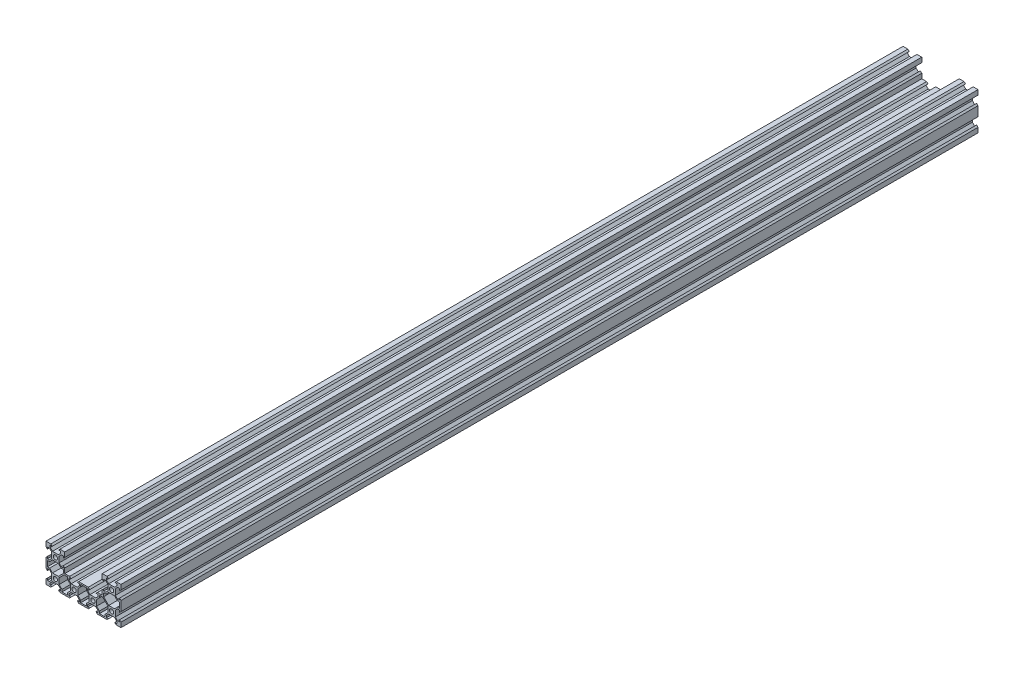
SolidWorks part; units mm, degrees
ref_plane "Front Plane" through (0, 0, 0) normal (0, 0, 1) x (1, 0, 0)
ref_plane "Top Plane" through (0, 0, 0) normal (0, 1, 0) x (1, 0, 0)
ref_plane "Right Plane" through (0, 0, 0) normal (1, 0, 0) x (0, 0, -1)
sketch "Sketch2" plane through (0, 0, 0) normal (0, 0, 1) x (1, 0, 0)
  line L0 (0, 10) -> (0, -10) construction
  line L1 (0, -10) -> (-40, -10)
  line L2 (-40, -10) -> (-40, 30)
  line L3 (-40, 30) -> (-20, 30)
  line L4 (-20, 30) -> (-20, 10)
  line L5 (-20, 10) -> (0, 10)
  line L6 (-20, 10) -> (-40, -10) construction
  line L7 (-20, 10) -> (0, -10) construction
  line L8 (0, 10) -> (-20, -10) construction
  line L9 (-20, -10) -> (-40, 10) construction
  line L10 (-40, 10) -> (-20, 30) construction
  line L12 (-40, 30) -> (-20, 10) construction
  line L13 (-35.5, 28.5) -> (-35.5, 25.5)
  line L14 (-40, 24.875) -> (-38.5, 23.375)
  line L15 (-40, 20) -> (-20, 20) construction
  line L16 (-40, 15.125) -> (-38.5, 16.625)
  line L17 (-30, 30) -> (-30, -10) construction
  line L18 (-33.375, 28.5) -> (-35.5, 28.5)
  line L19 (-38.5, 25.5) -> (-35.5, 25.5)
  line L20 (-34.875, 30) -> (-33.375, 28.5)
  line L21 (-38.5, 23.375) -> (-38.5, 25.5)
  line L22 (-38.5, 16.625) -> (-38.5, 14.5)
  line L23 (-38.5, 14.5) -> (-35.5, 14.5)
  line L24 (-25.125, 30) -> (-26.625, 28.5)
  line L25 (-26.625, 28.5) -> (-24.5, 28.5)
  line L26 (-20, 24.875) -> (-21.5, 23.375)
  line L27 (-21.5, 23.375) -> (-21.5, 25.5)
  line L28 (-21.5, 25.5) -> (-24.5, 25.5)
  line L29 (-24.5, 28.5) -> (-24.5, 25.5)
  line L30 (-20, 15.125) -> (-21.5, 16.625)
  line L31 (-21.5, 16.625) -> (-21.5, 14.5)
  line L32 (-21.5, 14.5) -> (-24.5, 14.5)
  line L33 (-40, 4.875) -> (-38.5, 3.375)
  line L34 (-38.5, 3.375) -> (-38.5, 5.5)
  line L35 (-38.5, 5.5) -> (-35.5, 5.5)
  line L36 (-25.125, -10) -> (-26.625, -8.5)
  line L37 (-26.625, -8.5) -> (-24.5, -8.5)
  line L38 (-24.5, -8.5) -> (-24.5, -5.5)
  line L39 (-34.875, -10) -> (-33.375, -8.5)
  line L40 (-35.5, -8.5) -> (-35.5, -5.5)
  line L41 (-33.375, -8.5) -> (-35.5, -8.5)
  line L42 (-40, -4.875) -> (-38.5, -3.375)
  line L43 (-38.5, -3.375) -> (-38.5, -5.5)
  line L44 (-38.5, -5.5) -> (-35.5, -5.5)
  line L45 (-26, 24) -> (-34, 24)
  line L46 (-26, 24) -> (-26, 16)
  line L47 (-34, 24) -> (-34, 16)
  line L48 (-34, 16) -> (-26, 16)
  line L49 (-35.5, 26.3839) -> (-33.1161, 24)
  line L50 (-36.3839, 25.5) -> (-34, 23.1161)
  line L51 (-23.6161, 25.5) -> (-26, 23.1161)
  line L52 (-24.5, 26.3839) -> (-26.8839, 24)
  line L53 (-23.6161, 14.5) -> (-26, 16.8839)
  line L54 (-38.5, 13) -> (-38.5, 7)
  line L55 (-38.5, 13) -> (-36.1161, 13)
  line L56 (-36.3839, 14.5) -> (-34, 16.8839)
  line L57 (-36.1161, 13) -> (-33.1161, 16)
  line L58 (-38.5, 7) -> (-36.1161, 7)
  line L59 (-36.1161, 7) -> (-33.1161, 4)
  line L60 (-26, -4) -> (-34, -4)
  line L61 (-34, -4) -> (-34, 4)
  line L62 (-26, -4) -> (-26, 4)
  line L63 (-34, 4) -> (-26, 4)
  line L64 (-26.891, 4) -> (-21.5, 9.391)
  line L65 (-23.8839, 13) -> (-26.8839, 16)
  line L66 (-21.5, 13) -> (-23.8839, 13)
  line L67 (-21.5, 13) -> (-21.5, 9.391)
  line L68 (-23, -6.1161) -> (-26, -3.1161)
  line L69 (-23, -8.5) -> (-23, -6.1161)
  line L70 (-17, -8.5) -> (-23, -8.5)
  line L71 (-17, -8.5) -> (-17, -6.1161)
  line L72 (-17, -6.1161) -> (-14, -3.1161)
  line L73 (-17, 6.1161) -> (-14, 3.1161)
  line L74 (-17, 8.5) -> (-17, 6.1161)
  line L75 (-17, 8.5) -> (-20.609, 8.5)
  line L76 (-26, 3.109) -> (-20.609, 8.5)
  line L77 (-36.3839, 5.5) -> (-34, 3.1161)
  line L78 (-36.3839, -5.5) -> (-34, -3.1161)
  line L79 (-35.5, -6.3839) -> (-33.1161, -4)
  line L80 (-24.5, -6.3839) -> (-26.8839, -4)
  line L81 (-5.125, 10) -> (-6.625, 8.5)
  line L82 (-4.5, 8.5) -> (-4.5, 5.5)
  line L83 (-6.625, 8.5) -> (-4.5, 8.5)
  line L84 (-4.5, 6.3839) -> (-6.8839, 4)
  line L85 (14.875, -10) -> (13.375, -8.5)
  line L86 (-15.5, -8.5) -> (-15.5, -5.5)
  line L87 (-14.875, -10) -> (-13.375, -8.5)
  line L88 (-13.375, -8.5) -> (-15.5, -8.5)
  line L89 (13.375, -8.5) -> (15.5, -8.5)
  line L90 (15.5, -8.5) -> (15.5, -5.5)
  line L91 (-5.125, -10) -> (-6.625, -8.5)
  line L92 (-6.625, -8.5) -> (-4.5, -8.5)
  line L93 (-4.5, -8.5) -> (-4.5, -5.5)
  line L94 (-15.5, -6.3839) -> (-13.1161, -4)
  line L95 (15.5, -6.3839) -> (13.1161, -4)
  line L96 (4.5, -6.3839) -> (6.8839, -4)
  line L97 (-4.5, -6.3839) -> (-6.8839, -4)
  line L98 (-6, -4) -> (-6, 4)
  line L99 (-14, -4) -> (-6, -4)
  line L100 (-14, -4) -> (-14, 4)
  line L101 (-6, 4) -> (-14, 4)
  line L102 (0, 0) -> (-40, 0) construction
  line L103 (-15.5, 6.3839) -> (-13.1161, 4)
  line L104 (-15.5, 8.5) -> (-15.5, 5.5)
  line L105 (-14.875, 10) -> (-13.375, 8.5)
  line L106 (-13.375, 8.5) -> (-15.5, 8.5)
  line L107 (-10, 10) -> (-10, -10) construction
  line L108 (4.5, -8.5) -> (4.5, -5.5)
  line L109 (6.625, -8.5) -> (4.5, -8.5)
  line L110 (5.125, -10) -> (6.625, -8.5)
  line L111 (17, 8.5) -> (20.609, 8.5)
  line L112 (17, 8.5) -> (17, 6.1161)
  line L113 (17, 6.1161) -> (14, 3.1161)
  line L114 (15.5, 6.3839) -> (13.1161, 4)
  line L115 (14.875, 10) -> (13.375, 8.5)
  line L116 (15.5, 8.5) -> (15.5, 5.5)
  line L117 (13.375, 8.5) -> (15.5, 8.5)
  line L118 (5.125, 10) -> (6.625, 8.5)
  line L119 (6.625, 8.5) -> (4.5, 8.5)
  line L120 (4.5, 8.5) -> (4.5, 5.5)
  line L121 (4.5, 6.3839) -> (6.8839, 4)
  line L122 (14, -4) -> (6, -4)
  line L123 (14, -4) -> (14, 4)
  line L124 (6, 4) -> (14, 4)
  line L125 (6, -4) -> (6, 4)
  line L126 (0, -10) -> (40, -10)
  line L127 (36.3839, 14.5) -> (34, 16.8839)
  line L128 (40, 15.125) -> (38.5, 16.625)
  line L129 (38.5, 16.625) -> (38.5, 14.5)
  line L130 (38.5, 14.5) -> (35.5, 14.5)
  line L131 (38.5, 7) -> (36.1161, 7)
  line L132 (38.5, 13) -> (38.5, 7)
  line L133 (40, 4.875) -> (38.5, 3.375)
  line L134 (38.5, 3.375) -> (38.5, 5.5)
  line L135 (38.5, 5.5) -> (35.5, 5.5)
  line L136 (36.3839, 5.5) -> (34, 3.1161)
  line L137 (36.1161, 7) -> (33.1161, 4)
  line L138 (38.5, 13) -> (36.1161, 13)
  line L139 (36.1161, 13) -> (33.1161, 16)
  line L140 (26, 24) -> (34, 24)
  line L141 (34, 24) -> (34, 16)
  line L142 (34, 16) -> (26, 16)
  line L143 (26, 24) -> (26, 16)
  line L144 (23.6161, 14.5) -> (26, 16.8839)
  line L145 (21.5, 16.625) -> (21.5, 14.5)
  line L146 (20, 15.125) -> (21.5, 16.625)
  line L147 (21.5, 14.5) -> (24.5, 14.5)
  line L148 (23.8839, 13) -> (26.8839, 16)
  line L149 (21.5, 13) -> (23.8839, 13)
  line L150 (21.5, 13) -> (21.5, 9.391)
  line L151 (26.891, 4) -> (21.5, 9.391)
  line L152 (26, 3.109) -> (20.609, 8.5)
  line L153 (38.5, -3.375) -> (38.5, -5.5)
  line L154 (40, -4.875) -> (38.5, -3.375)
  line L155 (36.3839, -5.5) -> (34, -3.1161)
  line L156 (38.5, -5.5) -> (35.5, -5.5)
  line L157 (35.5, -6.3839) -> (33.1161, -4)
  line L158 (35.5, -8.5) -> (35.5, -5.5)
  line L159 (34.875, -10) -> (33.375, -8.5)
  line L160 (33.375, -8.5) -> (35.5, -8.5)
  line L161 (34, 4) -> (26, 4)
  line L162 (34, -4) -> (34, 4)
  line L163 (26, -4) -> (34, -4)
  line L164 (26, -4) -> (26, 4)
  line L165 (23, -6.1161) -> (26, -3.1161)
  line L166 (23, -8.5) -> (23, -6.1161)
  line L167 (26.625, -8.5) -> (24.5, -8.5)
  line L168 (24.5, -8.5) -> (24.5, -5.5)
  line L169 (24.5, -6.3839) -> (26.8839, -4)
  line L170 (17, -6.1161) -> (14, -3.1161)
  line L171 (17, -8.5) -> (17, -6.1161)
  line L172 (17, -8.5) -> (23, -8.5)
  line L173 (40, -10) -> (40, 30)
  line L174 (36.3839, 25.5) -> (34, 23.1161)
  line L175 (35.5, 26.3839) -> (33.1161, 24)
  line L176 (40, 24.875) -> (38.5, 23.375)
  line L177 (38.5, 23.375) -> (38.5, 25.5)
  line L178 (38.5, 25.5) -> (35.5, 25.5)
  line L179 (35.5, 28.5) -> (35.5, 25.5)
  line L180 (33.375, 28.5) -> (35.5, 28.5)
  line L181 (34.875, 30) -> (33.375, 28.5)
  line L182 (25.125, 30) -> (26.625, 28.5)
  line L183 (26.625, 28.5) -> (24.5, 28.5)
  line L184 (24.5, 26.3839) -> (26.8839, 24)
  line L185 (24.5, 28.5) -> (24.5, 25.5)
  line L186 (23.6161, 25.5) -> (26, 23.1161)
  line L187 (21.5, 25.5) -> (24.5, 25.5)
  line L188 (21.5, 23.375) -> (21.5, 25.5)
  line L189 (20, 24.875) -> (21.5, 23.375)
  line L190 (40, 30) -> (20, 30)
  line L191 (0, 10) -> (20, 10)
  line L192 (20, 10) -> (20, 30)
  line L193 (3, 8.5) -> (-3, 8.5)
  line L194 (-3, 8.5) -> (-3, 6.1161)
  line L195 (-3, 6.1161) -> (-6, 3.1161)
  line L196 (3, 8.5) -> (3, 6.1161)
  line L197 (3, 6.1161) -> (6, 3.1161)
  line L198 (-3, -8.5) -> (-3, -6.1161)
  line L199 (-3, -6.1161) -> (-6, -3.1161)
  line L200 (3, -6.1161) -> (6, -3.1161)
  line L201 (3, -8.5) -> (3, -6.1161)
  line L202 (3, -8.5) -> (-3, -8.5)
  line L203 (25.125, -10) -> (26.625, -8.5)
  circle A0 centre (-30, 20) radius 2.25
  circle A1 centre (-30, 0) radius 2.25
  circle A2 centre (-10, 0) radius 2.25
  circle A3 centre (10, 0) radius 2.25
  circle A4 centre (30, 20) radius 2.25
  circle A5 centre (30, 0) radius 2.25
  point P3 (0, 0)
  point P75 (-38.5, 10)
  point P232 (25.125, -10)
  point P271 (0, 8.5)
  dimension "D8" = 4.5
  dimension "D1" = 40
  dimension "D2" = 40
  dimension "D3" = 20
  dimension "D4" = 4.5
  dimension "D5" = 3.375
  dimension "D6" = 1.5
  dimension "D7" = 8
  dimension "D9" = 0.625
  dimension "D10" = 0.625
  dimension "D11" = 1.5
  dimension "D12" = 0.63
  dimension "D13" = 40
  dimension "D14" = 40
  dimension "D15" = 20
  dimension "D16" = 3
  dimension "D17" = 1.5
  dimension "D18" = 0.625
extrude "Boss-Extrude1" add sketch "Sketch2" along normal blind 914.4
